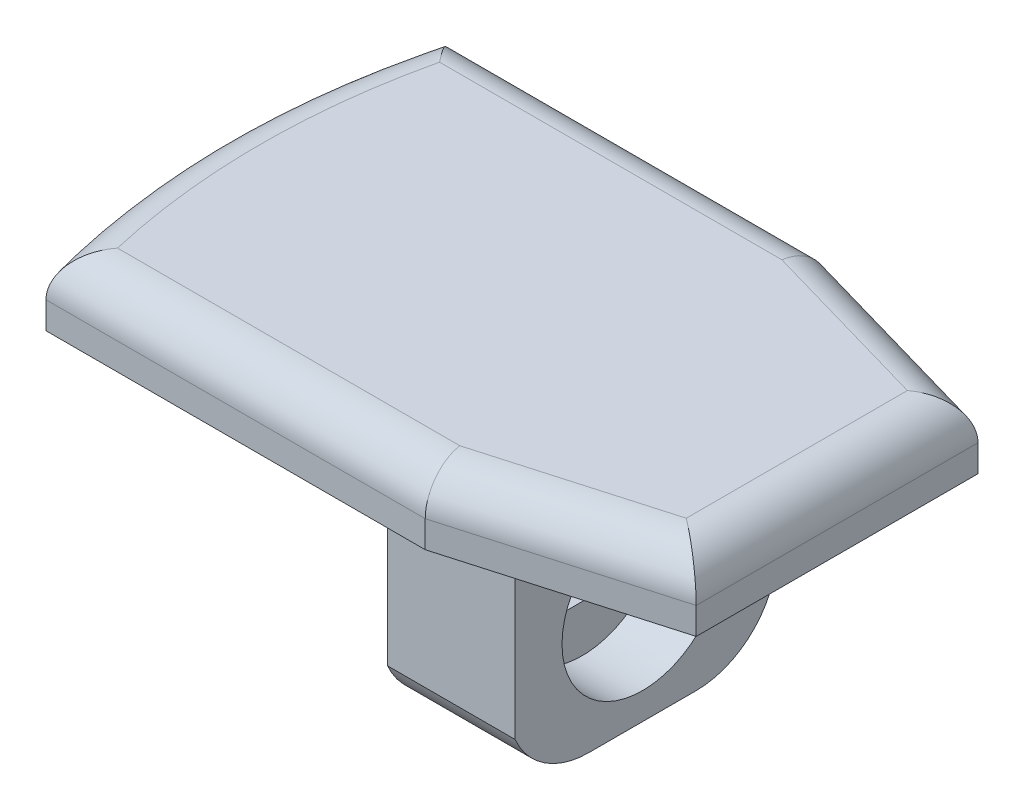
SolidWorks part; units mm, degrees
ref_plane "Front Plane" through (0, 0, 0) normal (0, 0, 1) x (1, 0, 0)
ref_plane "Top Plane" through (0, 0, 0) normal (0, 1, 0) x (1, 0, 0)
ref_plane "Right Plane" through (0, 0, 0) normal (1, 0, 0) x (0, 0, -1)
sketch "Sketch1" plane through (0, 0, 0) normal (0, 1, 0) x (1, 0, 0)
  line L0 (-34.3395, 50.6226) -> (-20.2094, 50.6226)
  line L1 (-20.2094, 50.6226) -> (-12.3627, 48.3726)
  line L2 (-12.3627, 48.3726) -> (-12.3627, 37.8726)
  line L3 (-12.3627, 37.8726) -> (-20.2094, 35.6226)
  line L4 (-20.2094, 35.6226) -> (-34.3395, 35.6226)
  line L5 (-29.3001, 48.1226) -> (-19.3627, 48.1226)
  line L6 (-19.3627, 48.1226) -> (-19.3627, 38.1226)
  line L7 (-19.3627, 38.1226) -> (-29.3001, 38.1226)
  circle A0 centre (-7.3627, 43.1226) radius 28
  circle A1 centre (-7.3627, 43.1226) radius 26
  point P13 (0, 0)
  point P14 (0, 0)
  point P15 (0, 0)
  point P16 (0, 0)
  point P17 (0, 0)
  point P18 (-34.3395, 50.6226)
  point P19 (-34.3395, 35.6226)
extrude "Boss-Extrude1" add sketch "Sketch1" along normal blind 2.5 contours L0 A1 L5 L6 L7 L4 L3 L2 L1 | A1 L0 A0 L4
ref_plane "Plane1" through (-12.3627, 0, -37.8726) normal (0, 0, 1) x (1, 0, 0)
sketch "Sketch4" plane through (0, 0, 0) normal (0, -1, 0) x (1, 0, 0)
  line L0 (-35.3627, -43.1226) -> (3.6803, -43.1226) construction
  line L1 (-12.3627, -48.3726) -> (-12.3627, -37.8726) construction
  line L2 (-32.8774, -38.1226) -> (-19.3627, -38.1226)
  line L3 (-19.3627, -38.1226) -> (-19.3627, -48.1226)
  line L4 (-19.3627, -48.1226) -> (-32.8774, -48.1226)
  arc A0 (-34.3395, -35.6226) -> (-34.3395, -50.6226) centre (-7.3627, -43.1226) ccw construction
  circle A1 centre (-7.3627, -43.1226) radius 26
  point P5 (-7.3627, -43.1226)
  dimension "D1" = 5
extrude "Boss-Extrude2" add sketch "Sketch4" along normal blind 1.5 and the other way blind 1.5
fillet "Fillet1" radius 1.5 6 edges at (-16.286, 2.5, -49.4976) (-12.3627, 2.5, -43.1226) (-16.286, 2.5, -36.7476) (-27.2745, 2.5, -35.6226) (-35.3627, 2.5, -43.1226) (-27.2745, 2.5, -50.6226)
sketch "Sketch5" plane through (0, -1.5, 0) normal (0, -1, 0) x (1, 0, 0)
  line L0 (-29.3001, -38.1226) -> (-19.3627, -38.1226) construction
  line L1 (-19.3627, -48.1226) -> (-24.3627, -48.1226)
  line L2 (-19.3627, -48.1226) -> (-19.3627, -38.1226)
  line L3 (-19.3627, -38.1226) -> (-24.3627, -38.1226)
  line L4 (-24.3627, -48.1226) -> (-24.3627, -38.1226)
  dimension "D1" = 5
extrude "Boss-Extrude3" add sketch "Sketch5" along normal blind 7.5
sketch "Sketch6" plane through (-19.3627, 0, 0) normal (1, 0, 0) x (0, 0, -1)
  line L0 (43.1226, 0) -> (43.1226, -9) construction
  line L1 (48.1226, 0) -> (38.1226, 0) construction
  line L2 (48.1226, -9) -> (38.1226, -9) construction
  circle A0 centre (43.1226, -5) radius 3
  dimension "D1" = 5
extrude "Cut-Extrude1" cut sketch "Sketch6" against normal blind 2.5
sketch "Sketch7" plane through (-21.8627, 0, 0) normal (1, 0, 0) x (0, 0, -1)
  line L1 (39.7279, -3.75) -> (47.1506, -3.75)
  line L2 (39.7279, -3.75) -> (39.7279, -6.25)
  line L3 (39.7279, -6.25) -> (47.1506, -6.25)
  line L4 (47.1506, -3.75) -> (47.1506, -6.25)
  circle A0 centre (43.1226, -5) radius 3
  circle M3 centre (43.1226, -5) radius 3
  dimension "D1" = 2.5
  dimension "D2" = 1.25
extrude "Cut-Extrude2" cut sketch "Sketch7" against normal blind 2.5 contours L3 L1 M3
fillet "Fillet2" radius 3 2 edges at (-21.8627, -9, -48.1226) (-21.8627, -9, -38.1226)
sketch "Sketch8" plane through (0, 0, 0) normal (0, -1, 0) x (1, 0, 0)
  line L0 (-19.3627, -48.1226) -> (-19.3627, -38.1226)
  line L1 (-19.3627, -38.1226) -> (-32.8774, -38.1226)
  line L2 (-19.3627, -48.1226) -> (-32.8774, -48.1226)
  line L3 (-19.6127, -47.8726) -> (-19.6127, -38.3726)
  line L4 (-19.6127, -38.3726) -> (-32.6708, -38.3726)
  line L5 (-19.6127, -47.8726) -> (-32.6708, -47.8726)
  arc A0 (-32.8774, -48.1226) -> (-32.8774, -38.1226) centre (-7.3627, -43.1226) cw
  arc A1 (-32.6708, -47.8726) -> (-32.6708, -38.3726) centre (-7.3627, -43.1226) cw
  dimension "D1" = 0.25
extrude "Cut-Extrude3" cut sketch "Sketch8" along normal blind 10
